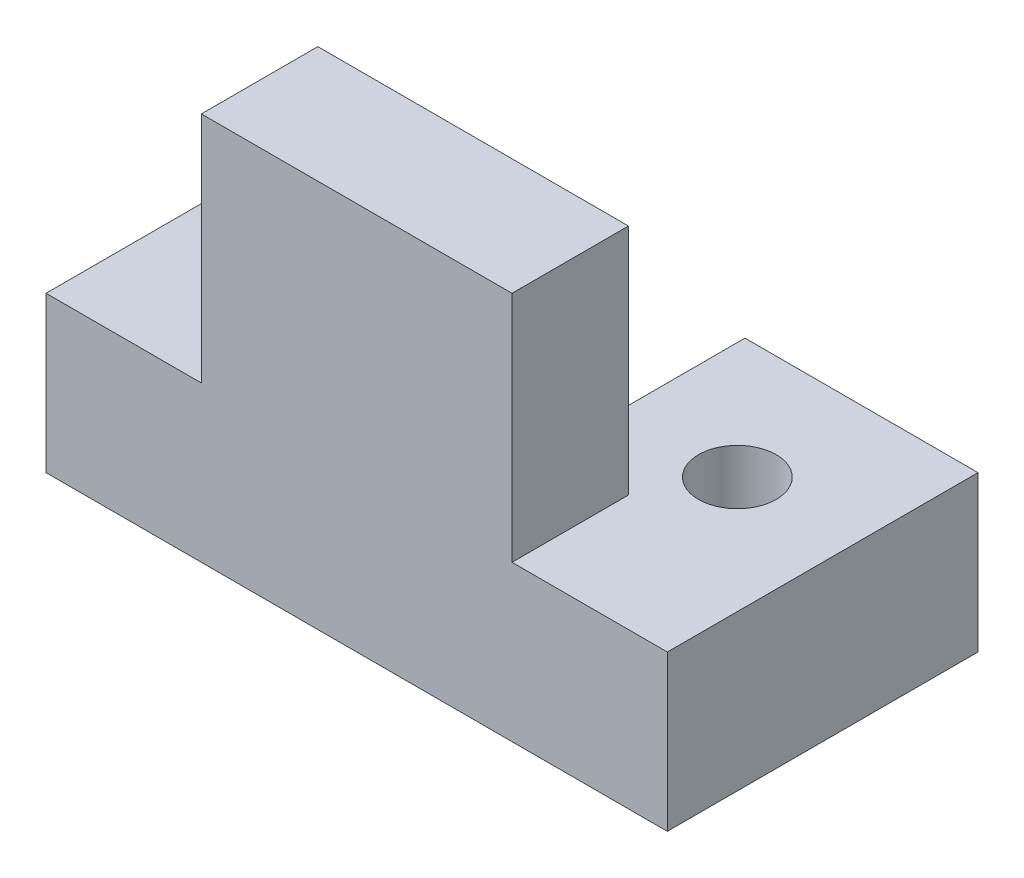
SolidWorks part; units mm, degrees
ref_plane "Front Plane" through (0, 0, 0) normal (0, 0, 1) x (1, 0, 0)
ref_plane "Top Plane" through (0, 0, 0) normal (0, 1, 0) x (1, 0, 0)
ref_plane "Right Plane" through (0, 0, 0) normal (1, 0, 0) x (0, 0, -1)
sketch "Sketch1" plane through (0, 0, 0) normal (0, 1, 0) x (1, 0, 0)
  line L1 (-58.4874, 105.0573) -> (43.1126, 105.0573)
  line L2 (-58.4874, 105.0573) -> (-58.4874, 54.2573)
  line L3 (-58.4874, 54.2573) -> (43.1126, 54.2573)
  line L4 (43.1126, 105.0573) -> (43.1126, 54.2573)
  line L5 (-58.4874, 105.0573) -> (43.1126, 54.2573) construction
  line L6 (-58.4874, 54.2573) -> (43.1126, 105.0573) construction
  point P0 (-7.6874, 79.6573)
extrude "Boss-Extrude1" add sketch "Sketch1" along normal blind 25.4
sketch "Sketch2" plane through (0, 25.4, 0) normal (0, 1, 0) x (1, 0, 0)
  line L0 (43.1126, 105.0573) -> (-58.4874, 105.0573) construction
  line L1 (-20.3874, 105.0573) -> (5.0126, 105.0573)
  line L2 (-20.3874, 105.0573) -> (-20.3874, 86.0073)
  line L3 (-20.3874, 86.0073) -> (5.0126, 86.0073)
  line L4 (5.0126, 105.0573) -> (5.0126, 86.0073)
  line L5 (-20.3874, 105.0573) -> (5.0126, 86.0073) construction
  line L6 (-20.3874, 86.0073) -> (5.0126, 105.0573) construction
  line L7 (-58.4874, 105.0573) -> (-58.4874, 54.2573) construction
  point P0 (-7.6874, 95.5323)
  dimension "D1" = 19.05
  dimension "D2" = 25.4
  dimension "D3" = 38.1
extrude "Cut-Extrude1" cut sketch "Sketch2" against normal through all
sketch "Sketch5" plane through (0, 25.4, 0) normal (0, 1, 0) x (1, 0, 0)
  line L0 (-58.4874, 54.2573) -> (43.1126, 54.2573) construction
  line L1 (-33.0874, 73.3073) -> (17.7126, 73.3073)
  line L2 (-33.0874, 73.3073) -> (-33.0874, 54.2573)
  line L3 (-33.0874, 54.2573) -> (17.7126, 54.2573)
  line L4 (17.7126, 73.3073) -> (17.7126, 54.2573)
  point P4 (-7.6874, 54.2573)
  dimension "D1" = 19.05
  dimension "D2" = 50.8
sketch "Sketch6" plane through (0, 25.4, 0) normal (0, 1, 0) x (1, 0, 0)
extrude "Boss-Extrude3" add sketch "Sketch5" along normal blind 38.1
sketch "Sketch7" plane through (0, 25.4, 0) normal (0, 1, 0) x (1, 0, 0)
  line L0 (43.1126, 54.2573) -> (43.1126, 105.0573) construction
  line L1 (43.1126, 105.0573) -> (5.0126, 105.0573) construction
  circle A0 centre (24.0626, 84.7557) radius 6.35
  point P6 (0, 0)
  dimension "D1" = 19.05
  dimension "D2" = 20.3016
  dimension "D3" = 12.7
extrude "Cut-Extrude2" cut sketch "Sketch7" against normal through all contours A0
